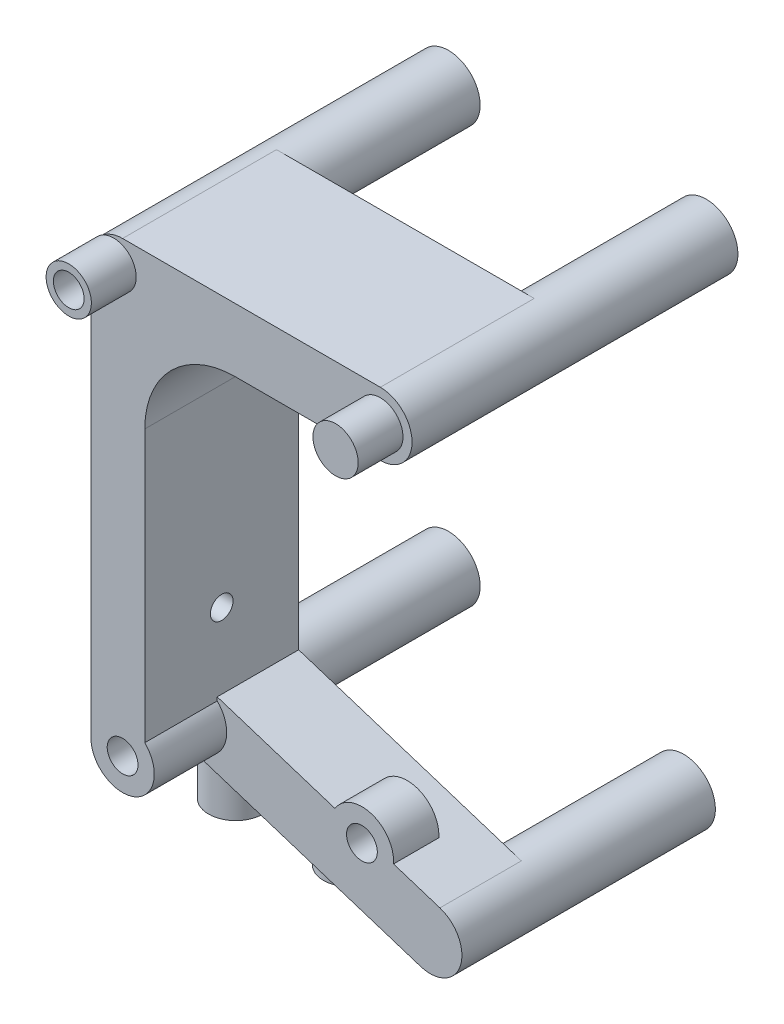
SolidWorks part; units mm, degrees
ref_plane "Ebene vorne" through (0, 0, 0) normal (0, 0, 1) x (1, 0, 0)
ref_plane "Ebene oben" through (0, 0, 0) normal (0, 1, 0) x (1, 0, 0)
ref_plane "Ebene rechts" through (0, 0, 0) normal (1, 0, 0) x (0, 0, -1)
sketch "Skizze1" plane through (0, 0, 0) normal (0, 0, 1) x (1, 0, 0)
  line L0 (0, -95) -> (0, -55.8609) construction
  line L2 (-16.5833, -95) -> (16.5833, -95) construction
  line L3 (34.9972, -57.1919) -> (64.2875, -57.1919) construction
  line L4 (64.2875, -57.1919) -> (70.5214, -61.0492) construction
  line L5 (70.5214, -61.0492) -> (56.68, -104.2087) construction
  circle A0 centre (50.05, -80.2019) radius 3.5
  circle A2 centre (50.05, -34.1819) radius 3.5
  circle A3 centre (78.525, -34.1819) radius 3.5
  circle A4 centre (76.0355, -88.5355) radius 3.5
  point P0 (-50.05, -80.2019)
  point P4 (-78.525, -34.1819)
  point P5 (-50.05, -34.1819)
  point P8 (76.0355, -88.5355)
  point P10 (-76.0355, -88.5355)
  point P11 (50.05, -34.1819)
  point P15 (78.525, -34.1819)
  point P16 (50.05, -80.2019)
  dimension "D1" = 7
extrude "Aufsatz-Linear austragen1" add sketch "Skizze1" along normal up to surface (36 mm away)
sketch "Skizze2" plane through (0, 0, 36) normal (0, 0, 1) x (1, 0, 0)
  line L0 (50.05, -30.6819) -> (78.525, -30.6819)
  line L1 (78.525, -37.6819) -> (52.5, -37.6819)
  line L4 (74.9667, -91.8683) -> (48.9812, -83.5347)
  line L5 (46.55, -80.2019) -> (46.55, -34.1819)
  line L6 (-52.5, -77.312) -> (-46.55, -77.312) construction
  line L7 (-52.5, -47.6819) -> (-52.5, -77.7024) construction
  line L8 (-46.55, -80.2019) -> (-46.55, -34.1819) construction
  line L9 (0, -45.0849) -> (0, -56.6032) construction
  line L10 (52.5, -37.6819) -> (52.5, -77.312)
  line L11 (52.5, -77.312) -> (77.1044, -85.2027)
  line L12 (52.5, -77.312) -> (46.55, -77.312) construction
  line L13 (-60.8815, -80) -> (-52.5, -77.312) construction
  line L14 (-52.5, -47.6819) -> (-52.5, -77.7024) construction
  arc A0 (77.1044, -85.2027) -> (74.9667, -91.8683) centre (76.0355, -88.5355) cw
  arc A1 (48.9812, -83.5347) -> (46.55, -80.2019) centre (50.05, -80.2019) cw
  arc A2 (46.55, -34.1819) -> (50.05, -30.6819) centre (50.05, -34.1819) cw
  arc A3 (78.525, -30.6819) -> (78.525, -37.6819) centre (78.525, -34.1819) cw
  circle A4 centre (78.525, -34.1819) radius 3.5 construction
  circle A5 centre (50.05, -34.1819) radius 3.5 construction
  circle A6 centre (50.05, -80.2019) radius 3.5 construction
  circle A7 centre (76.0355, -88.5355) radius 3.5 construction
extrude "Aufsatz-Linear austragen2" add sketch "Skizze2" against normal up to surface (17 mm away)
sketch "Skizze3" plane through (52.5, 0, 0) normal (1, 0, 0) x (0, 0, -1)
  circle A0 centre (-27.5, -69) radius 1.25
  dimension "D1" = 2.5
extrude "Schnitt-Linear austragen1" cut sketch "Skizze3" against normal through all
sketch "Skizze4" plane through (0, 0, 0) normal (0, 0, -1) x (-1, 0, 0)
  line L0 (-64.2875, -21.2774) -> (-64.2875, -57.1919) construction
  line L1 (-64.2875, -57.1919) -> (-71.7585, -57.1919) construction
  line L2 (-71.7585, -57.1919) -> (-65.6003, -76.3939) construction
  circle A0 centre (-78.525, -34.1819) radius 2.1
  circle A1 centre (-78.525, -34.1819) radius 3.5 construction
  circle A2 centre (-50.05, -34.1819) radius 2.1
  circle A3 centre (-50.05, -34.1819) radius 3.5 construction
  circle A4 centre (-50.05, -80.2019) radius 2.1
  circle A5 centre (-76.0355, -88.5355) radius 2.1
  dimension "D1" = 4.2
extrude "Schnitt-Linear austragen2" cut sketch "Skizze4" against normal blind 4.2
sketch "Skizze5" plane through (0, 0, 36) normal (0, 0, 1) x (1, 0, 0)
  line L2 (74.9667, -91.8683) -> (48.9812, -83.5347)
  line L4 (48.9812, -83.5347) -> (74.9667, -91.8683) construction
  line L5 (52.5, -77.7024) -> (52.5, -77.312)
  line L6 (52.5, -77.312) -> (77.1044, -85.2027)
  line L7 (77.1044, -85.2027) -> (52.5, -77.312) construction
  line L8 (52.5, -77.312) -> (52.5, -37.6819) construction
  arc A0 (52.5, -77.7024) -> (48.9812, -83.5347) centre (50.05, -80.2019) cw
  arc A1 (77.1044, -85.2027) -> (74.9667, -91.8683) centre (76.0355, -88.5355) cw
  arc A2 (74.9667, -91.8683) -> (77.1044, -85.2027) centre (76.0355, -88.5355) ccw construction
  arc A5 (48.9812, -83.5347) -> (46.55, -80.2019) centre (50.05, -80.2019) ccw construction
extrude "Schnitt-Linear austragen3" cut sketch "Skizze5" against normal blind 8
fillet "Verrundung1" radius 10 1 edges at (52.5, -37.6819, 27.5)
sketch "Skizze11" plane through (0, -89.47, 0) normal (0, 1, 0) x (1, 0, 0)
  line L0 (51.09, -21.54) -> (-63.79, -21.54) construction
  line L1 (57.44, -27.504) -> (57.44, -20.432) construction
  circle A0 centre (51.09, -24.54) radius 3
  circle A2 centre (63.79, -24.54) radius 3
  circle A3 centre (-63.79, -24.54) radius 3 construction
extrude "Aufsatz-Linear austragen3" add sketch "Skizze11" along normal up to surface (9.47 mm away)
sketch "Skizze12" plane through (0, 0, 28) normal (0, 0, 1) x (1, 0, 0)
  line L0 (60.8815, -80) -> (66.79, -81.8949)
  line L1 (77.1044, -85.2027) -> (52.5, -77.312) construction
  line L2 (66.79, -81.8949) -> (66.79, -80)
  line L3 (66.79, -80) -> (60.8815, -80) construction
  line L4 (66.79, -80) -> (60.8815, -80)
  line L7 (66.79, -81.8949) -> (66.79, -80) construction
  line L8 (66.79, -80) -> (60.8815, -80) construction
extrude "Schnitt-Linear austragen7" cut sketch "Skizze12" against normal through all
sketch "Skizze13" plane through (0, 0, 28) normal (0, 0, 1) x (1, 0, 0)
  circle A0 centre (68.49, -83.32) radius 3.5
  arc A2 (69.43, -79.9486) -> (65.4073, -84.9773) centre (68.49, -83.32) ccw construction
extrude "Aufsatz-Linear austragen4" add sketch "Skizze13" against normal blind 5
sketch "Skizze14" plane through (0, 0, 28) normal (0, 0, 1) x (1, 0, 0)
  circle A0 centre (68.49, -83.32) radius 1.7
  arc A1 (71.9818, -83.5599) -> (65.51, -81.4844) centre (68.49, -83.32) ccw construction
  dimension "D1" = 3.4
extrude "Schnitt-Linear austragen8" cut sketch "Skizze14" against normal blind 4
sketch "Skizze15" plane through (0, 0, 36) normal (0, 0, 1) x (1, 0, 0)
  circle A0 centre (50.05, -80.2019) radius 1.7
  arc A1 (46.55, -80.2019) -> (52.5, -77.7024) centre (50.05, -80.2019) ccw construction
  dimension "D1" = 3.4
extrude "Schnitt-Linear austragen9" cut sketch "Skizze15" against normal blind 4
sketch "Skizze16" plane through (0, -89.47, 0) normal (0, -1, 0) x (-1, 0, 0)
  line L0 (-57.44, -31.4256) -> (-57.44, -14.9264) construction
  circle A0 centre (-51.09, -24.54) radius 1.7
  circle A1 centre (-51.09, -24.54) radius 3 construction
  circle A2 centre (-63.79, -24.54) radius 1.7
  circle A3 centre (-63.79, -24.54) radius 3 construction
  dimension "D1" = 3.4
extrude "Schnitt-Linear austragen10" cut sketch "Skizze16" against normal blind 4
sketch "Skizze20" plane through (0, 0, 36) normal (0, 0, 1) x (1, 0, 0)
  line L0 (46.55, -64.1819) -> (46.55, -30.6819) construction
  line L1 (63.3219, -58.8576) -> (63.2291, -63.834) construction
  circle A0 centre (49.05, -33.6319) radius 2.5
  circle A1 centre (78.525, -34.1819) radius 2.5
extrude "Aufsatz-Linear austragen5" add sketch "Skizze20" along normal up to surface (4.95 mm away)
sketch "Skizze21" plane through (0, 0, 40.95) normal (0, 0, 1) x (1, 0, 0)
  circle A0 centre (49.05, -33.6319) radius 1.7
  circle A1 centre (49.05, -33.6319) radius 2.5 construction
  dimension "D1" = 3.4
extrude "Schnitt-Linear austragen13" cut sketch "Skizze21" against normal blind 4
equation "\"M2EinschmelzGewindeDurchmesser\"=3.4"
equation "\"M2EinschmelzGewindeTiefe\"= 4.0"
equation "\"M3EinschmelzGewindeDurchmesser\"= 4.2"
equation "\"M3EinschmelzGewindeTief\"= 5.7"
equation "\"M2SchraubeLoch\"=2.3"
equation "\"M3SchraubeLoch\"=3.3"
equation "\"offSetVonGummiReifen\"= 3.0"
equation "\"D1@Skizze4\"=\"M3EinschmelzGewindeDurchmesser\""
equation "\"D1@Schnitt-Linear austragen2\"=\"M3EinschmelzGewindeDurchmesser\""
equation "\"D1@Skizze14\"=\"M2EinschmelzGewindeDurchmesser\""
equation "\"D1@Schnitt-Linear austragen8\"=\"M2EinschmelzGewindeTiefe\""
equation "\"D1@Skizze15\"=\"M2EinschmelzGewindeDurchmesser\""
equation "\"D1@Schnitt-Linear austragen9\"=\"M2EinschmelzGewindeTiefe\""
equation "\"D1@Skizze16\"=\"M2EinschmelzGewindeDurchmesser\""
equation "\"D1@Schnitt-Linear austragen10\"=\"M2EinschmelzGewindeTiefe\""
equation "\"D1@Skizze21\"=\"M2EinschmelzGewindeDurchmesser\""
equation "\"D1@Schnitt-Linear austragen13\"=\"M2EinschmelzGewindeTiefe\""
